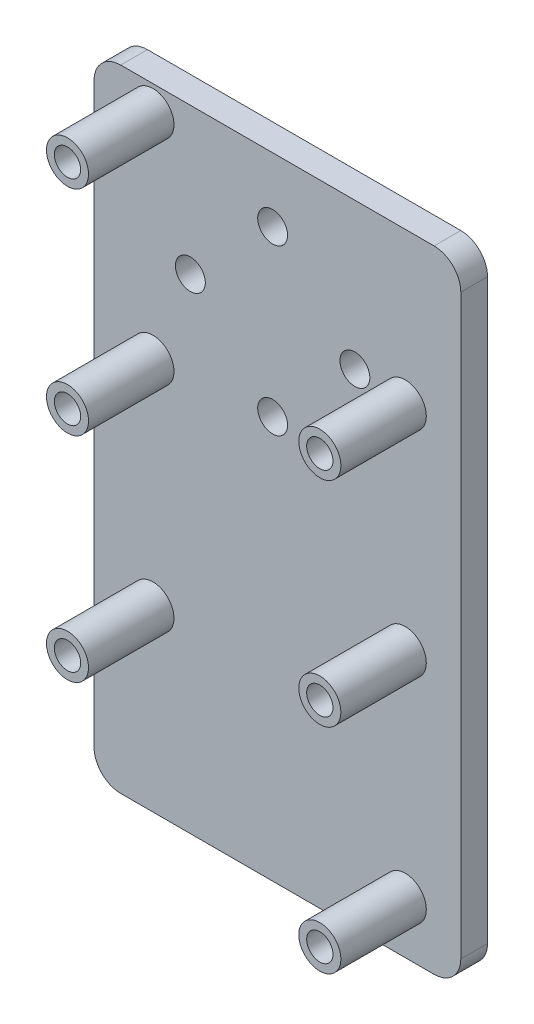
SolidWorks part; units mm, degrees
material "Copper"
ref_plane "Front Plane" through (0, 0, 0) normal (0, 0, 1) x (1, 0, 0)
ref_plane "Top Plane" through (0, 0, 0) normal (0, 1, 0) x (1, 0, 0)
ref_plane "Right Plane" through (0, 0, 0) normal (1, 0, 0) x (0, 0, -1)
sketch "Sketch1" plane through (0, 0, 0) normal (0, 0, 1) x (1, 0, 0)
  line L1 (0, 0) -> (43.6, 0)
  line L2 (0, 0) -> (0, -75)
  line L3 (0, -75) -> (43.6, -75)
  line L4 (43.6, 0) -> (43.6, -75)
  dimension "D1" = 43.6
  dimension "D2" = 75
extrude "Boss-Extrude1" add sketch "Sketch1" along normal blind 3.175
sketch "Sketch2" plane through (0, 0, 3.175) normal (0, 0, 1) x (1, 0, 0)
  line L0 (43.6, 0) -> (0, 0) construction
  line L1 (0, 0) -> (0, -75) construction
  circle A0 centre (37, -18) radius 2.5
  circle A1 centre (7, -3) radius 2.5
  circle A2 centre (7, -3) radius 1.5635
  circle A3 centre (37, -18) radius 1.5635
  dimension "D1" = 5
  dimension "D2" = 5
  dimension "D7" = 3.127
  dimension "D8" = 3.127
  dimension "D3" = 30
  dimension "D4" = 15
  dimension "D5" = 3
  dimension "D6" = 7
extrude "Boss-Extrude2" add sketch "Sketch2" along normal blind 10.16
sketch "Sketch3" plane through (0, 0, 3.175) normal (0, 0, 1) x (1, 0, 0)
  circle A0 centre (7, -3) radius 1.5635
  circle A1 centre (37, -18) radius 1.5635
  dimension "D1" = 3.127
  dimension "D2" = 3.127
extrude "Cut-Extrude1" cut sketch "Sketch3" against normal blind 10.16
pattern_linear "LPattern1" count 3 spacing 25.4 along (0, -1, 0) of "Boss-Extrude2", "Cut-Extrude1"
sketch "Sketch4" plane through (0, 0, 3.175) normal (0, 0, 1) x (1, 0, 0)
  circle A0 centre (7, -28.4) radius 1.5635
  circle A1 centre (37, -43.4) radius 1.5635
  circle A2 centre (37, -68.8) radius 1.5635
  circle A3 centre (7, -53.8) radius 1.5635
  dimension "D1" = 3.127
  dimension "D2" = 3.127
  dimension "D3" = 3.127
  dimension "D4" = 3.127
extrude "Cut-Extrude3" cut sketch "Sketch4" along normal mid plane 20.32
sketch "Sketch5" plane through (0, 0, 3.175) normal (0, 0, 1) x (1, 0, 0)
  line L0 (43.6, 0) -> (0, 0) construction
  line L1 (0, 0) -> (0, -75) construction
  circle A0 centre (21.2289, -7.62) radius 1.778
  circle A1 centre (21.2289, -27.178) radius 1.778
  circle A2 centre (11.4499, -17.399) radius 1.778
  circle A3 centre (31.0079, -17.399) radius 1.778
  point P12 (0, 0)
  dimension "D1" = 3.556
  dimension "D2" = 3.556
  dimension "D3" = 3.556
  dimension "D4" = 3.556
  dimension "D5" = 19.558
  dimension "D6" = 19.558
  dimension "D7" = 9.779
  dimension "D8" = 9.779
  dimension "D9" = 7.62
  dimension "D10" = 11.4499
  dimension "D11" = 9.779
  dimension "D12" = 21.2289
extrude "Cut-Extrude4" cut sketch "Sketch5" against normal blind 20.32
fillet "Fillet1" radius 3.175 4 edges at (0, 0, 1.5875) (43.6, 0, 1.5875) (43.6, -75, 1.5875) (0, -75, 1.5875)
